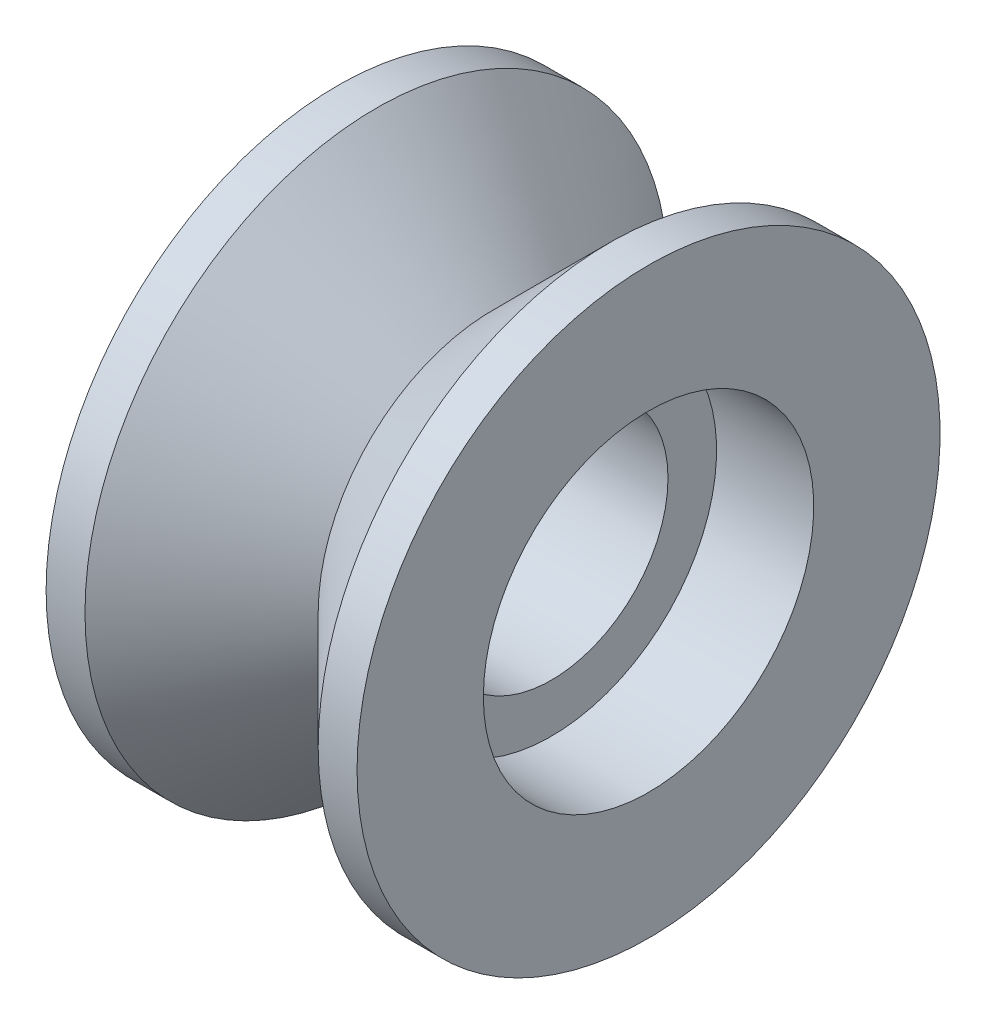
SolidWorks part; units mm, degrees
material "Nailon 101"
ref_plane "Alzado" through (0, 0, 0) normal (0, 0, 1) x (1, 0, 0)
ref_plane "Planta" through (0, 0, 0) normal (0, 1, 0) x (1, 0, 0)
ref_plane "Vista lateral" through (0, 0, 0) normal (1, 0, 0) x (0, 0, -1)
sketch "Croquis1" plane through (0, 0, 0) normal (0, 0, 1) x (1, 0, 0)
  line L0 (0, 0) -> (24.9796, 0) construction
  line L1 (0, 8.5) -> (5, 8.5)
  line L2 (5, 8.5) -> (5, 6)
  line L3 (5, 6) -> (11, 6)
  line L4 (8, 6) -> (8, 9) construction
  line L5 (8, 9) -> (2, 15)
  line L6 (2, 15) -> (0, 15)
  line L7 (0, 15) -> (0, 8.5)
  line L8 (11, 8.5) -> (11, 6)
  line L9 (8, 9) -> (14, 15)
  line L10 (14, 15) -> (16, 15)
  line L11 (16, 15) -> (16, 8.5)
  line L12 (16, 8.5) -> (11, 8.5)
  dimension "D1" = 17
  dimension "D2" = 12
  dimension "D3" = 5
  dimension "D4" = 3
  dimension "D5" = 30
  dimension "D6" = 45
  dimension "D7" = 2
revolve "Revolución1" add sketch "Croquis1" angle 360 about L0
